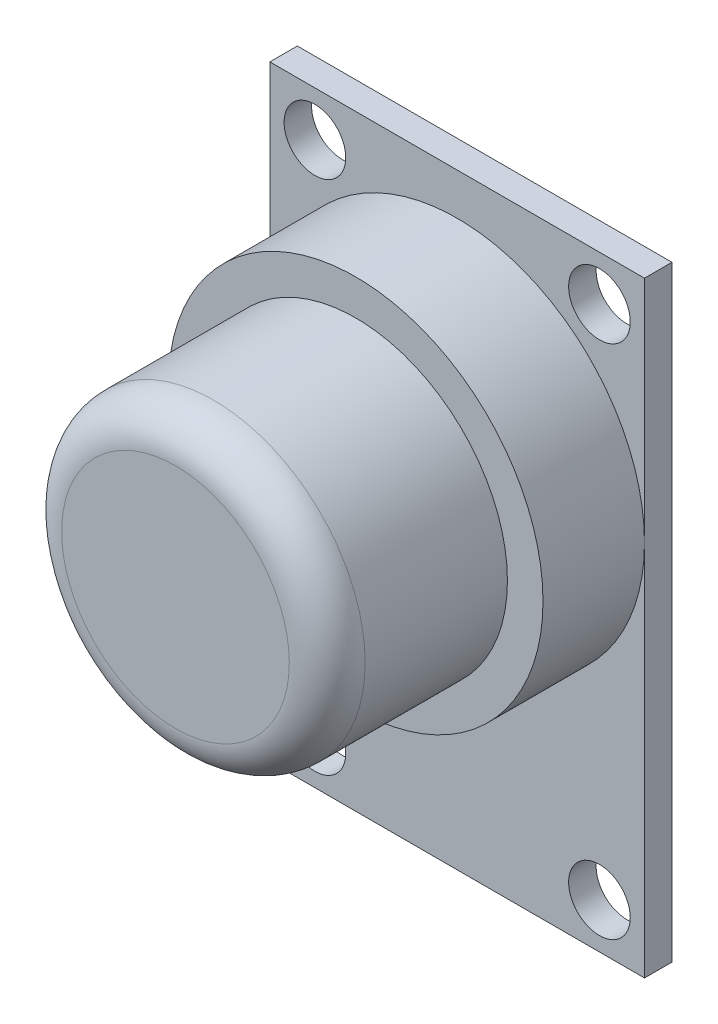
SolidWorks part; units mm, degrees
ref_plane "Front Plane" through (0, 0, 0) normal (0, 0, 1) x (1, 0, 0)
ref_plane "Top Plane" through (0, 0, 0) normal (0, 1, 0) x (1, 0, 0)
ref_plane "Right Plane" through (0, 0, 0) normal (1, 0, 0) x (0, 0, -1)
sketch "Sketch1" plane through (0, 0, 0) normal (0, 0, 1) x (1, 0, 0)
  line L1 (-9.875, 15.975) -> (9.875, 15.975)
  line L2 (-9.875, 15.975) -> (-9.875, -15.975)
  line L3 (-9.875, -15.975) -> (9.875, -15.975)
  line L4 (9.875, 15.975) -> (9.875, -15.975)
  line L5 (-9.875, 15.975) -> (9.875, -15.975) construction
  line L6 (-9.875, -15.975) -> (9.875, 15.975) construction
  point P0 (0, 0)
  dimension "D1" = 19.75
  dimension "D2" = 31.95
extrude "Boss-Extrude1" add sketch "Sketch1" along normal blind 1.45
sketch "Sketch2" plane through (0, 0, 1.45) normal (0, 0, 1) x (1, 0, 0)
  line L1 (0.7975, 0) -> (-0.7975, 0) construction
  line L3 (0, -0.7975) -> (0, 0.7975) construction
  circle A0 centre (-7.5, 13.6) radius 1.625
  circle A1 centre (-7.5, -13.6) radius 1.625
  circle A2 centre (7.5, -13.6) radius 1.625
  circle A3 centre (7.5, 13.6) radius 1.625
extrude "Cut-Extrude1" cut sketch "Sketch2" against normal through all
sketch "Sketch3" plane through (0, 0, 1.45) normal (0, 0, 1) x (1, 0, 0)
  circle A0 centre (0, 3.9) radius 9.875
extrude "Boss-Extrude2" add sketch "Sketch3" along normal blind 5.35
sketch "Sketch4" plane through (0, 0, 6.8) normal (0, 0, 1) x (1, 0, 0)
  circle A1 centre (0, 3.9) radius 8
  dimension "D1" = 16
extrude "Boss-Extrude3" add sketch "Sketch4" along normal blind 9.5
fillet "Fillet1" radius 2 1 edges at (8, 3.9, 16.3)
